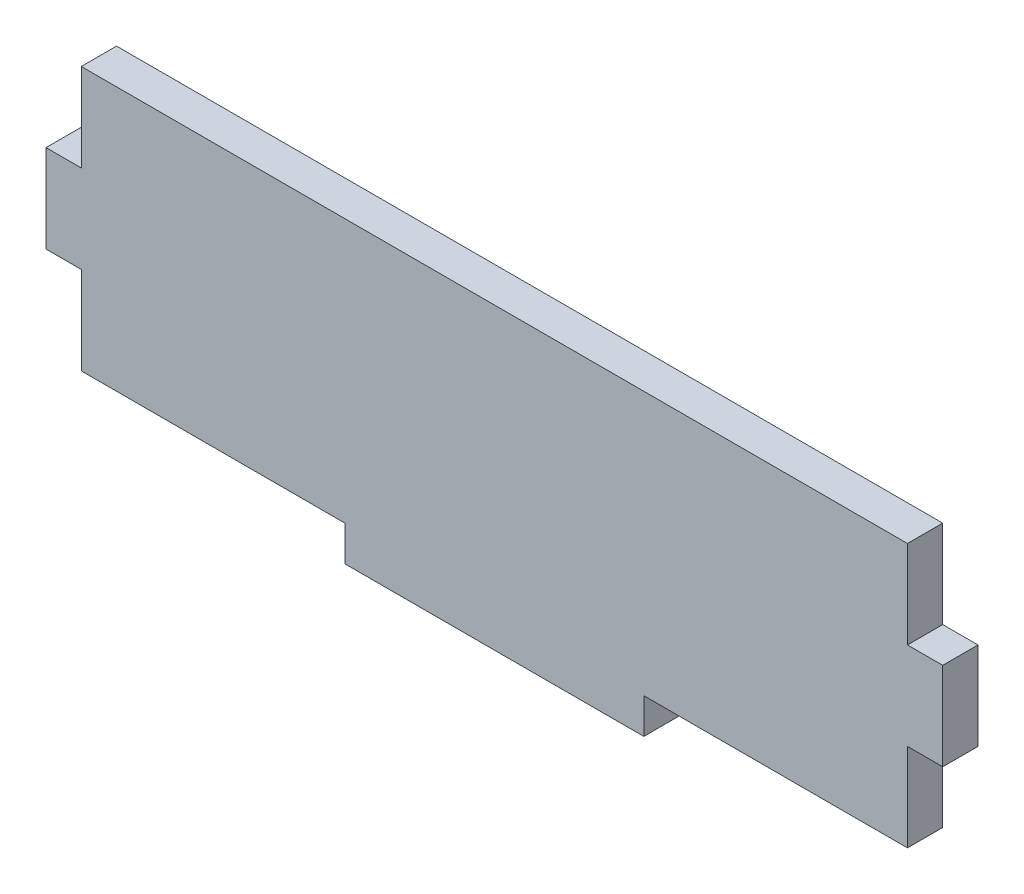
SolidWorks part; units mm, degrees
ref_plane "Front Plane" through (0, 0, 0) normal (0, 0, 1) x (1, 0, 0)
ref_plane "Top Plane" through (0, 0, 0) normal (0, 1, 0) x (1, 0, 0)
ref_plane "Right Plane" through (0, 0, 0) normal (1, 0, 0) x (0, 0, -1)
sketch "Sketch1" plane through (0, 0, 0) normal (0, 0, 1) x (1, 0, 0)
  line L1 (21.813, 7.872) -> (47.213, 7.872)
  line L2 (-3.587, 18.3368) -> (-3.587, 25.8044)
  line L3 (-0.5898, 33.272) -> (69.6158, 33.272)
  line L4 (72.613, 18.3368) -> (72.613, 25.8044)
  line L7 (-0.5898, 10.8692) -> (21.813, 10.8692)
  line L8 (21.813, 7.872) -> (21.813, 10.8692)
  line L9 (-3.587, 18.3368) -> (-0.5898, 18.3368)
  line L10 (-0.5898, 10.8692) -> (-0.5898, 18.3368)
  line L11 (69.6158, 10.8692) -> (47.213, 10.8692)
  line L12 (47.213, 7.872) -> (47.213, 10.8692)
  line L13 (-3.587, 25.8044) -> (-0.5898, 25.8044)
  line L14 (-0.5898, 33.272) -> (-0.5898, 25.8044)
  line L17 (72.613, 18.3368) -> (69.6158, 18.3368)
  line L18 (69.6158, 10.8692) -> (69.6158, 18.3368)
  line L21 (72.613, 25.8044) -> (69.6158, 25.8044)
  line L22 (69.6158, 33.272) -> (69.6158, 25.8044)
  dimension "height" = 25.4
  dimension "tabDepth" = 2.9972
  dimension "length" = 76.2
  dimension "bottomTab" = 25.4
  dimension "bottomTapSpace" = 25.4
extrude "Boss-Extrude1" add sketch "Sketch1" along normal blind 2.9972
